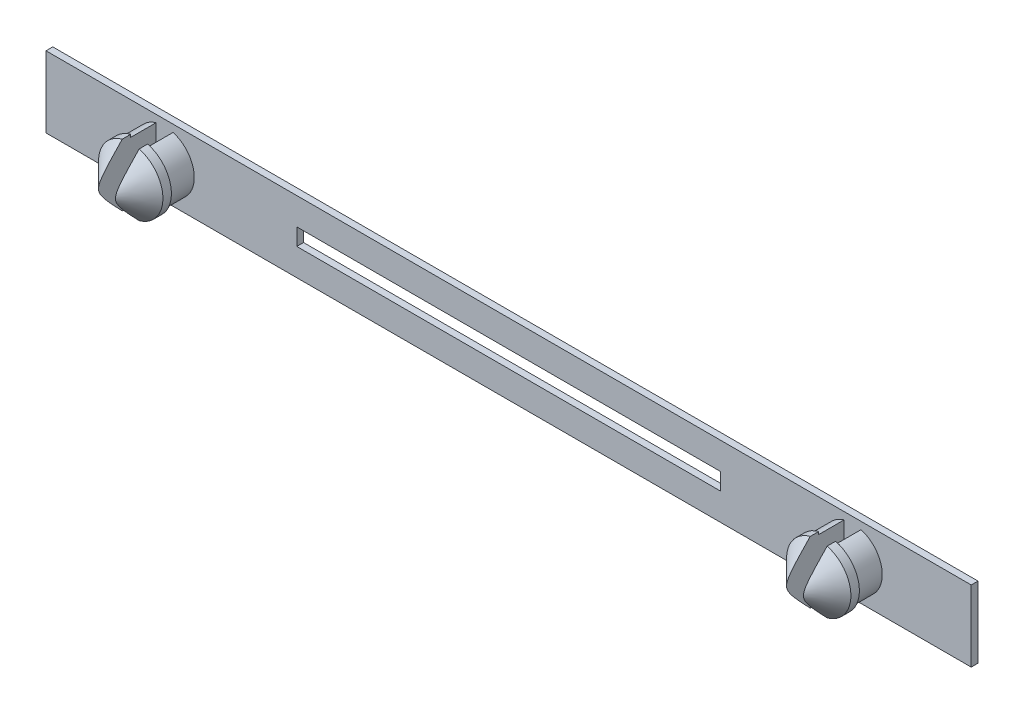
SolidWorks part; units mm, degrees
ref_plane "Přední rovina" through (0, 0, 0) normal (0, 0, 1) x (1, 0, 0)
ref_plane "Horní rovina" through (0, 0, 0) normal (0, 1, 0) x (1, 0, 0)
ref_plane "Pravá rovina" through (0, 0, 0) normal (1, 0, 0) x (0, 0, -1)
sketch "Skica2" plane through (0, 0, 0) normal (0, 0, 1) x (1, 0, 0)
  line L1 (-27.3, 2.1) -> (27.3, 2.1)
  line L2 (-27.3, 2.1) -> (-27.3, -2.1)
  line L3 (-27.3, -2.1) -> (27.3, -2.1)
  line L4 (27.3, 2.1) -> (27.3, -2.1)
  line L5 (-27.3, 2.1) -> (27.3, -2.1) construction
  line L6 (-27.3, -2.1) -> (27.3, 2.1) construction
  line L7 (12.5, 0.5) -> (-12.5, 0.5)
  line L8 (12.5, 0.5) -> (12.5, -0.5)
  line L9 (12.5, -0.5) -> (-12.5, -0.5)
  line L10 (-12.5, 0.5) -> (-12.5, -0.5)
  line L11 (12.5, 0.5) -> (-12.5, -0.5) construction
  line L12 (12.5, -0.5) -> (-12.5, 0.5) construction
  point P0 (0, 0)
  point P5 (0, 0)
  point P11 (0, 0)
  point P12 (0, 0)
  dimension "D1" = 4.2
  dimension "D2" = 54.6
  dimension "D3" = 1
  dimension "D4" = 25
  dimension "D5" = 14.8
  dimension "D6" = 14.8
  dimension "D7" = 0
extrude "Přidat vysunutím2" add sketch "Skica2" along normal blind 0.4
sketch "Skica3" plane through (0, 0, 0.4) normal (0, 0, 1) x (1, 0, 0)
  line L0 (-27.3, 2.1) -> (-27.3, -2.1) construction
  line L1 (27.3, -2.1) -> (27.3, 2.1) construction
  line L2 (27.3, 2.1) -> (-27.3, 2.1) construction
  line L3 (-27.3, -2.1) -> (27.3, -2.1) construction
  circle A0 centre (-20.3, 0) radius 1.75
  circle A1 centre (20.3, 0) radius 1.75
  dimension "D1" = 3.5
  dimension "D3" = 3.5
  dimension "D2" = 7
  dimension "D4" = 7
  dimension "D5" = 2.1
  dimension "D6" = 2.1
extrude "Přidat vysunutím3" add sketch "Skica3" along normal blind 1.5
sketch "Skica5" plane through (0, 0, 1.9) normal (0, 0, 1) x (1, 0, 0)
  circle A0 centre (-20.3, 0) radius 1.9
  circle A1 centre (20.3, 0) radius 1.9
  dimension "D1" = 3.8
  dimension "D2" = 3.8
extrude "Přidat vysunutím5" add sketch "Skica5" along normal blind 2
chamfer "Zkosení2" distance 1.5 angle 45 2 edges at (22.2, 0, 3.9) (-18.4, 0, 3.9)
sketch "Skica7" plane through (0, 0, 3.9) normal (0, 0, 1) x (1, 0, 0)
  line L1 (-19.8, 2.5) -> (-20.8, 2.5)
  line L2 (-19.8, 2.5) -> (-19.8, -2.5)
  line L3 (-19.8, -2.5) -> (-20.8, -2.5)
  line L4 (-20.8, 2.5) -> (-20.8, -2.5)
  line L5 (-19.8, 2.5) -> (-20.8, -2.5) construction
  line L6 (-19.8, -2.5) -> (-20.8, 2.5) construction
  line L7 (19.8, 2.5) -> (20.8, 2.5)
  line L8 (19.8, 2.5) -> (19.8, -2.5)
  line L9 (19.8, -2.5) -> (20.8, -2.5)
  line L10 (20.8, 2.5) -> (20.8, -2.5)
  line L11 (19.8, 2.5) -> (20.8, -2.5) construction
  line L12 (19.8, -2.5) -> (20.8, 2.5) construction
  point P0 (-20.3, 0)
  point P5 (20.3, 0)
  dimension "D1" = 5
  dimension "D2" = 1
  dimension "D3" = 5
  dimension "D4" = 1
extrude "Odebrat vysunutím1" cut sketch "Skica7" against normal blind 3.5
equation "\"1.5.000mm\"=10"
